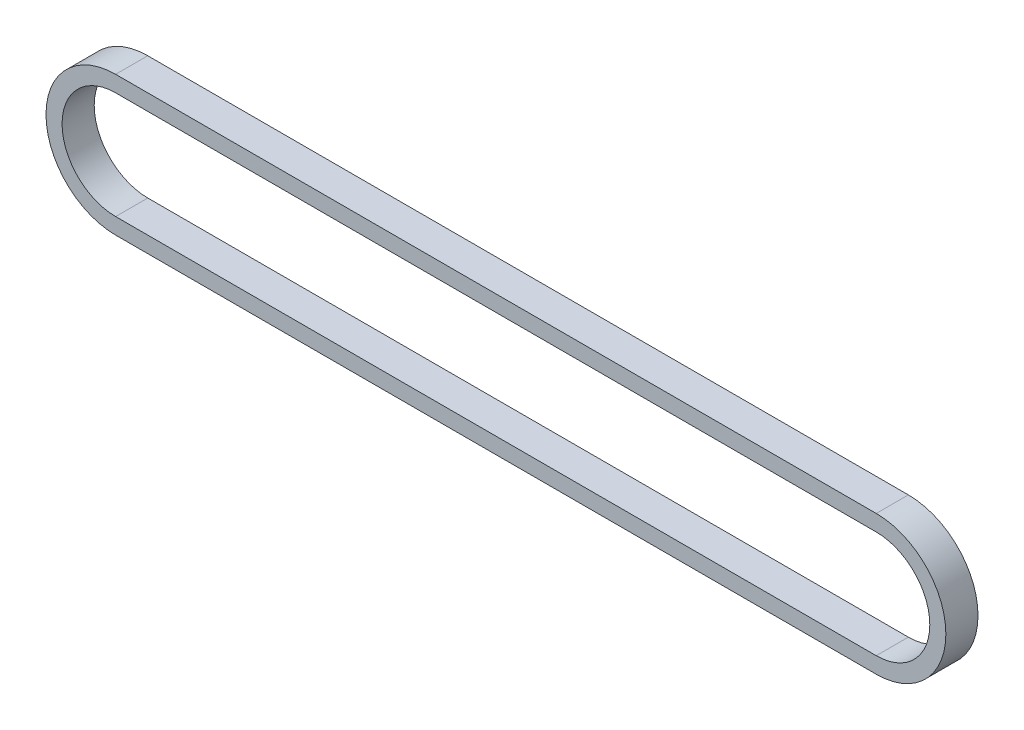
SolidWorks part; units mm, degrees
material "Rubber"
ref_plane "Front Plane" through (0, 0, 0) normal (0, 0, 1) x (1, 0, 0)
ref_plane "Top Plane" through (0, 0, 0) normal (0, 1, 0) x (1, 0, 0)
ref_plane "Right Plane" through (0, 0, 0) normal (1, 0, 0) x (0, 0, -1)
sketch "Sketch1" plane through (0, 0, 0) normal (0, 0, 1) x (1, 0, 0)
  line L0 (-35.5, 0) -> (35.5, 0) construction
  line L1 (-35.5, 5) -> (35.5, 5)
  line L2 (-35.5, -5) -> (35.5, -5)
  line L3 (-35.5, 0) -> (35.5, 0) construction
  line L4 (-35.5, 6.5) -> (35.5, 6.5)
  line L5 (-35.5, -6.5) -> (35.5, -6.5)
  arc A0 (-35.5, 5) -> (-35.5, -5) centre (-35.5, 0) ccw
  arc A1 (35.5, -5) -> (35.5, 5) centre (35.5, 0) ccw
  arc A2 (-35.5, 6.5) -> (-35.5, -6.5) centre (-35.5, 0) ccw
  arc A3 (35.5, -6.5) -> (35.5, 6.5) centre (35.5, 0) ccw
  point P2 (0, 0)
  point P9 (0, 0)
  dimension "D2" = 6.5
  dimension "D3" = 1.5
  dimension "D1" = 71
extrude "Boss-Extrude1" add sketch "Sketch1" along normal blind 3
